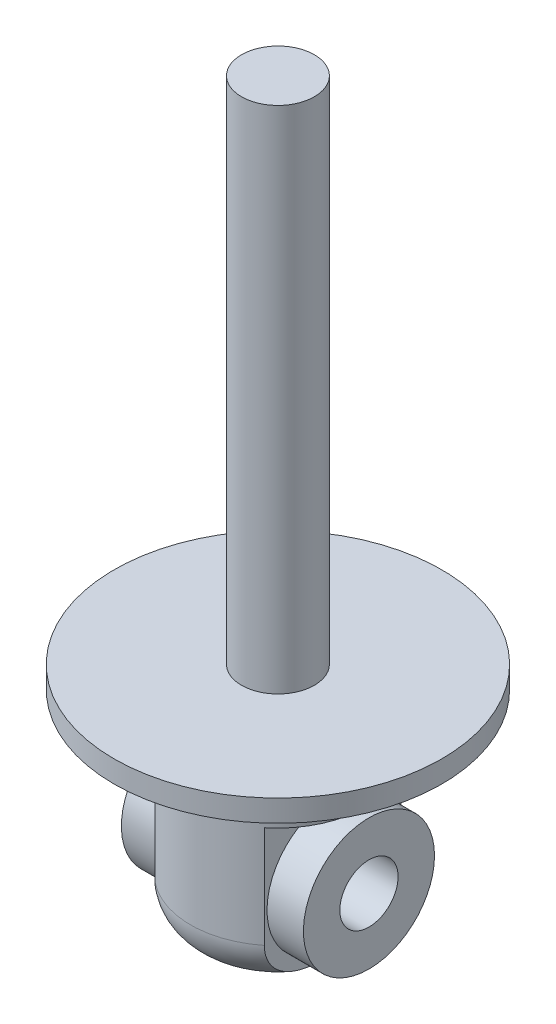
SolidWorks part; units mm, degrees
ref_plane "Front Plane" through (0, 0, 0) normal (0, 0, 1) x (1, 0, 0)
ref_plane "Top Plane" through (0, 0, 0) normal (0, 1, 0) x (1, 0, 0)
ref_plane "Right Plane" through (0, 0, 0) normal (1, 0, 0) x (0, 0, -1)
sketch "Sketch1" plane through (0, 0, 0) normal (0, 1, 0) x (1, 0, 0)
  circle A0 centre (0, 0) radius 22.5
  dimension "D1" = 45
extrude "Boss-Extrude1" add sketch "Sketch1" along normal blind 3
sketch "Sketch2" plane through (0, 3, 0) normal (0, 1, 0) x (1, 0, 0)
  circle A0 centre (0, 0) radius 5
  dimension "D1" = 10
extrude "Boss-Extrude2" add sketch "Sketch2" along normal blind 70
sketch "Sketch3" plane through (0, 0, 0) normal (0, -1, 0) x (1, 0, 0)
  circle A0 centre (0, 0) radius 12
  dimension "D1" = 24
extrude "Boss-Extrude3" add sketch "Sketch3" along normal blind 28
fillet "Fillet1" radius 6 1 edges at (0, -28, -12)
sketch "Sketch4" plane through (0, 0, 0) normal (0, 0, 1) x (1, 0, 0)
  line L0 (0, 0) -> (0, -29.9353) construction
  line L1 (7.5, -28) -> (27.4834, -28)
  line L3 (27.4834, -28) -> (27.4834, -8)
  line L4 (27.4834, -8) -> (7.5, -8)
  line L5 (7.5, -8) -> (7.5, -28)
  line L6 (-7.5, -8) -> (-7.5, -28)
  line L7 (-27.4834, -8) -> (-7.5, -8)
  line L8 (-27.4834, -28) -> (-27.4834, -8)
  line L9 (-7.5, -28) -> (-27.4834, -28)
  dimension "D1" = 15
  dimension "D2" = 20
  dimension "D3" = 27.4834
  dimension "D4" = 8
extrude "Cut-Extrude1" cut sketch "Sketch4" against normal through all both and the other way through all
sketch "Sketch5" plane through (7.5, 0, 0) normal (1, 0, 0) x (0, 0, -1)
  line L0 (0, 0) -> (0, -28) construction
  line L1 (-6, -28) -> (6, -28) construction
  circle A0 centre (0, -18) radius 4
  dimension "D1" = 8
  dimension "D2" = 10
extrude "Cut-Extrude2" cut sketch "Sketch5" against normal through all both
sketch "Sketch7" plane through (0, 0, 0) normal (1, 0, 0) x (0, 0, -1)
  circle A0 centre (0, -18) radius 9
  circle A1 centre (0, -18) radius 4 construction
  circle A2 centre (0, -18) radius 4
  dimension "D1" = 18
extrude "Boss-Extrude5" add sketch "Sketch7" along normal mid plane 25
